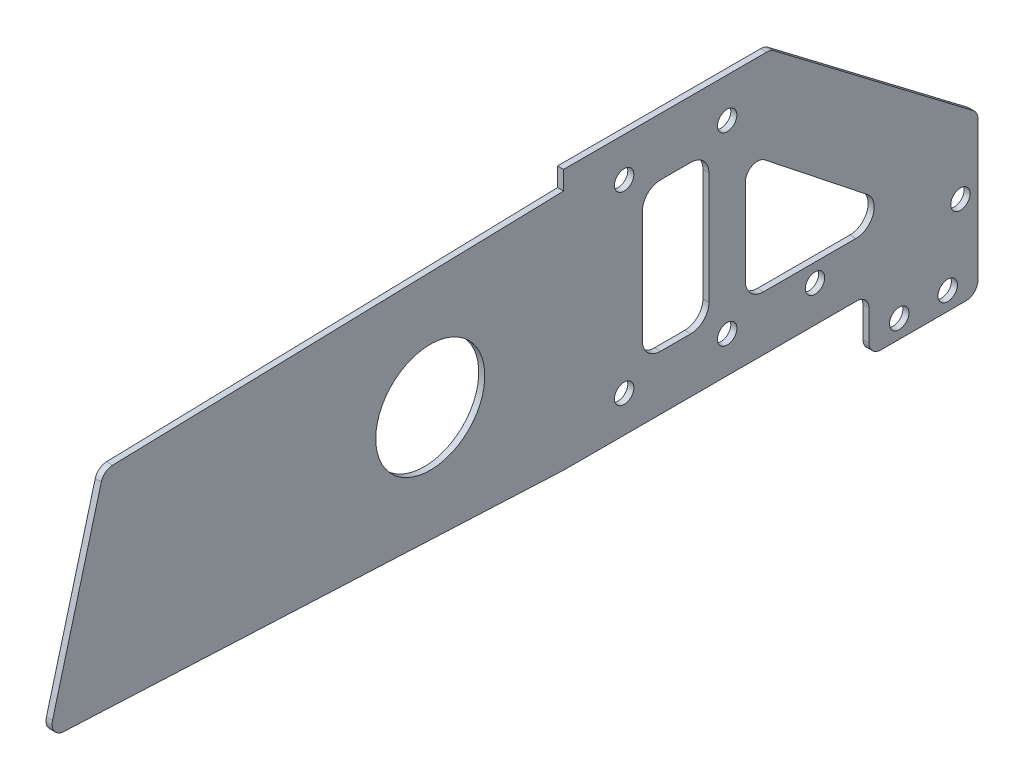
SolidWorks part; units mm, degrees
material "Hexcel AS4C (3000 丝)"
ref_plane "前视基准面" through (0, 0, 0) normal (0, 0, 1) x (1, 0, 0)
ref_plane "上视基准面" through (0, 0, 0) normal (0, 1, 0) x (1, 0, 0)
ref_plane "右视基准面" through (0, 0, 0) normal (1, 0, 0) x (0, 0, -1)
sketch "草图1" plane through (0, 0, 0) normal (1, 0, 0) x (0, 0, -1)
  line L0 (0, 0) -> (17, 0) construction
  line L1 (0, 0) -> (0, -30.5) construction
  line L2 (17, -30.5) -> (31.5, -30.5) construction
  line L4 (-10, 7.5) -> (48, 7.5)
  line L5 (-10, 7.5) -> (-10, -36.5)
  line L6 (-10, -36.5) -> (48, -36.5)
  line L7 (48, 7.5) -> (48, -36.5)
  line L8 (19, -36.5) -> (19, 7.5) construction
  line L9 (-10, -14.5) -> (48, -14.5) construction
  circle A0 centre (0, 0) radius 1.6
  circle A1 centre (17, 0) radius 1.6
  circle A2 centre (0, -30.5) radius 1.6
  circle A3 centre (17, -30.5) radius 1.6
  circle A4 centre (31.5, -30.5) radius 1.6
  point P257 (19, -14.5)
  dimension "D1" = 3.2
  dimension "D2" = 17
  dimension "D5" = 30.5
  dimension "D6" = 14.5
  dimension "D7" = 6
  dimension "D8" = 10
  dimension "D9" = 58
  dimension "D10" = 44
  dimension "D3" = 2
  dimension "D4" = 2
extrude "凸台-拉伸1" add sketch "草图1" along normal blind 1
sketch "草图2" plane through (1, 0, 0) normal (1, 0, 0) x (0, 0, -1)
  line L0 (-10, 7.5) -> (-10, -36.5) construction
  line L1 (48, 7.5) -> (-84.5, 7.5)
  line L2 (48, 7.5) -> (48, 97.5)
  line L3 (48, 97.5) -> (-84.5, 97.5)
  line L4 (-84.5, 7.5) -> (-84.5, 97.5)
  line L5 (-18.25, 97.5) -> (-18.25, 7.5) construction
  line L6 (48, 52.5) -> (-84.5, 52.5) construction
  point P288 (-18.25, 52.5)
  dimension "D1" = 90
  dimension "D2" = 74.5
extrude "凸台-拉伸2" add sketch "草图2" against normal up to surface (1 mm away) up to face at (0, -14.5, -19)
sketch "草图3" [suppressed] plane through (0, 0, 0) normal (-1, 0, 0) x (0, 0, 1)
  line L0 (86.5, 7.5) -> (62.3846, 97.5)
  line L1 (86.5, 97.5) -> (-48, 97.5) construction
  line L2 (62.3846, 97.5) -> (86.5, 97.5)
  line L3 (86.5, 97.5) -> (86.5, 7.5)
  dimension "D1" = 15
extrude "切除-拉伸1" [suppressed] cut sketch "草图3" against normal through all
sketch "草图4" [suppressed] plane through (0, 0, 0) normal (-1, 0, 0) x (0, 0, 1)
  line L0 (85.6962, 10.5) -> (-48, 10.5) construction
  line L1 (62.3846, 97.5) -> (86.5, 7.5) construction
  line L2 (-48, -36.5) -> (-48, 97.5) construction
  line L3 (12, 7.5) -> (86.5, 7.5) construction
  line L4 (71.5, 10.5) -> (51.5, 10.5) construction
  line L5 (63.1884, 94.5) -> (-48, 94.5) construction
  line L6 (62.3846, 97.5) -> (86.5, 7.5) construction
  line L7 (-48, -36.5) -> (-48, 97.5) construction
  line L8 (-48, 97.5) -> (62.3846, 97.5) construction
  circle A0 centre (71.5, 10.5) radius 1.6
  circle A1 centre (51.5, 10.5) radius 1.6
  circle A2 centre (12, 94.5) radius 1.6
  circle A3 centre (32, 94.5) radius 1.6
  dimension "D2" = 3.2
  dimension "D6" = 3.2
  dimension "D1" = 3
  dimension "D3" = 15
  dimension "D4" = 20
  dimension "D5" = 3
  dimension "D7" = 20
  dimension "D8" = 60
extrude "切除-拉伸2" [suppressed] cut sketch "草图4" against normal through all
sketch "草图5" [suppressed] plane through (1, 0, 0) normal (1, 0, 0) x (0, 0, -1)
  line L0 (-86.5, 7.5) -> (-12, 7.5) construction
  line L1 (-26.5, 60.5) -> (9.5, 60.5) construction
  line L2 (-26.5, 60.5) -> (-26.5, 24.5) construction
  line L3 (-26.5, 24.5) -> (9.5, 24.5) construction
  line L4 (9.5, 60.5) -> (9.5, 24.5) construction
  line L5 (-8.5, 24.5) -> (-8.5, 60.5) construction
  line L6 (-26.5, 42.5) -> (9.5, 42.5) construction
  circle A0 centre (-26.5, 60.5) radius 1.35
  circle A1 centre (9.5, 60.5) radius 1.35
  circle A2 centre (9.5, 24.5) radius 1.35
  circle A3 centre (-26.5, 24.5) radius 1.35
  point P0 (-8.5, 42.5)
  dimension "D2" = 2.7
  dimension "D1" = 36
  dimension "D3" = 35
  dimension "D4" = 60
extrude "切除-拉伸3" [suppressed] cut sketch "草图5" against normal through all
sketch "草图6" plane through (1, 0, 0) normal (1, 0, 0) x (0, 0, -1)
  line L0 (-84.5, 7.5) -> (-10, 7.5) construction
  line L1 (48, 97.5) -> (33, 97.5)
  line L2 (48, 97.5) -> (48, 7.5)
  line L3 (48, 7.5) -> (33, 7.5)
  line L4 (33, 97.5) -> (33, 7.5)
  line L5 (40.5, 7.5) -> (40.5, 97.5) construction
  line L6 (48, 52.5) -> (33, 52.5) construction
  point P304 (40.5, 52.5)
  dimension "D1" = 15
extrude "切除-拉伸4" cut sketch "草图6" against normal through all and the other way through all
sketch "草图7" plane through (1, 0, 0) normal (1, 0, 0) x (0, 0, -1)
  line L1 (0, 0) -> (17, 0) construction
  line L2 (0, 0) -> (0, -30.5) construction
  line L3 (0, -30.5) -> (17, -30.5) construction
  line L4 (17, 0) -> (17, -30.5) construction
  line L5 (8.5, -30.5) -> (8.5, 0) construction
  line L6 (0, -15.25) -> (17, -15.25) construction
  line L8 (4, -4) -> (13, -4)
  line L9 (4, -4) -> (4, -26.5)
  line L10 (4, -26.5) -> (13, -26.5)
  line L11 (13, -4) -> (13, -26.5)
  line L12 (8.5, -26.5) -> (8.5, -4) construction
  line L13 (4, -15.25) -> (13, -15.25) construction
  point P5 (8.5, -15.25)
  point P144 (8.5, -15.25)
  dimension "D1" = 4
  dimension "D2" = 4
extrude "切除-拉伸5" [suppressed] cut sketch "草图7" against normal through all
fillet "圆角1" [suppressed] radius 2
sketch "草图8" plane through (1, 0, 0) normal (1, 0, 0) x (0, 0, -1)
  line L0 (-10, 7.5) -> (33, 7.5)
  line L2 (48, 7.5) -> (-10, 7.5)
  line L3 (48, 7.5) -> (48, 6.5)
  line L4 (48, 6.5) -> (-10, 6.5)
  line L5 (-10, 7.5) -> (-10, 6.5)
  line L7 (-10, 7.5) -> (-10, -36.5) construction
  line L14 (-84.5, 97.5) -> (-84.5, 7.5)
  line L15 (33, 7.5) -> (33, 97.5)
  line L16 (-84.5, 97.5) -> (-84.5, 7.5)
  line L17 (33, 97.5) -> (-84.5, 97.5)
  line L21 (-84.5, 7.5) -> (-10, 7.5)
  line L22 (-10, 7.5) -> (-10, -36.5)
  line L24 (-10, -36.5) -> (48, -36.5)
  line L26 (48, -36.5) -> (48, 7.5)
  line L28 (48, 7.5) -> (33, 7.5)
  line L29 (33, 7.5) -> (33, 97.5)
  line L31 (33, 97.5) -> (-84.5, 97.5)
  line L35 (-84.5, 7.5) -> (-10, 7.5)
  dimension "D2" = 1
  dimension "D1" = 0
extrude "切除-拉伸6" cut sketch "草图8" against normal through all
sketch "草图9" plane through (1, 0, 0) normal (1, 0, 0) x (0, 0, -1)
  line L0 (-10, 3.4) -> (-85.9165, 1.4)
  line L1 (-10, 6.5) -> (-10, -36.5) construction
  line L2 (-85.9165, 1.4) -> (-95, -32.5)
  line L3 (-95, -32.5) -> (-10, -32.5) construction
  line L4 (-10, 3.4) -> (-10, -32.5)
  line L5 (48, 6.5) -> (-10, 6.5) construction
  line L7 (-10, -36.5) -> (48, -36.5) construction
  line L8 (-95, -32.5) -> (-10, -36.5)
  line M20 (-10, 6.5) -> (-10, -36.5)
  dimension "D1" = 3.1
  dimension "D2" = 85
  dimension "D3" = 75
  dimension "D4" = 4
  dimension "D5" = 2
extrude "凸台-拉伸3" add sketch "草图9" against normal up to surface (1 mm away) contours L2 L3 L0 M20 | L3 L8 M20 up to face at (0, -30.5, -33.1)
sketch "草图10" plane through (1, 0, 0) normal (1, 0, 0) x (0, 0, -1)
  line L3 (48, 6.5) -> (-10, 6.5) construction
  line L4 (40.4, -45.5) -> (58.4, -45.5)
  line L5 (40.4, -36.5) -> (40.4, -45.5)
  line L6 (-10, -36.5) -> (48, -36.5) construction
  line L8 (58.4, -45.5) -> (58.4, 6.5)
  line L9 (58.4, 6.5) -> (48, 6.5)
  line L11 (48, -36.5) -> (48, 6.5) construction
  line L12 (48, -36.5) -> (48, 6.5)
  line L13 (40.4, -36.5) -> (48, -36.5)
  dimension "D1" = 10.4
  dimension "D2" = 9
  dimension "D3" = 18
extrude "凸台-拉伸4" add sketch "草图10" against normal up to surface (1 mm away) up to face at (0, -30.5, -33.1)
sketch "草图11" plane through (1, 0, 0) normal (1, 0, 0) x (0, 0, -1)
  line L1 (40.4, -45.5) -> (58.4, -45.5) construction
  line L2 (58.4, -45.5) -> (58.4, 6.5) construction
  circle A0 centre (45.4, -42.5) radius 1.6
  circle A1 centre (53.4, -42.5) radius 1.6
  dimension "D1" = 3.2
  dimension "D2" = 5
  dimension "D3" = 8
  dimension "D4" = 3
extrude "切除-拉伸7" cut sketch "草图11" against normal through all
fillet "圆角4" [suppressed] radius 1
sketch "草图13" plane through (1, 0, 0) normal (1, 0, 0) x (0, 0, -1)
  line L0 (24.2, 6.5) -> (58.4, -19.5)
  line L1 (58.4, 6.5) -> (-10, 6.5) construction
  line L2 (58.4, -45.5) -> (58.4, 6.5) construction
  line L3 (58.4, -19.5) -> (58.4, 6.5)
  line L4 (58.4, 6.5) -> (24.2, 6.5)
extrude "切除-拉伸8" cut sketch "草图13" against normal through all
fillet "圆角3" radius 2 7 edges at (0.5, 1.4, 85.9165) (0.5, -36.5, -40.4) (0.5, -45.5, -58.4) (0.5, -45.5, -40.4) (0.5, -32.5, 95) (0.5, -19.5, -58.4) (0.5, 6.5, -24.2)
sketch "草图14" plane through (1, 0, 0) normal (1, 0, 0) x (0, 0, -1)
  line L0 (31.5, -30.5) -> (-49968.5, -30.5) construction
  line L1 (58.4, -43.5) -> (58.4, -20.4919) construction
  circle A0 centre (55.5, -30.5) radius 1.6
  circle A1 centre (31.5, -30.5) radius 1.6 construction
  dimension "D1" = 2.9
extrude "切除-拉伸9" cut sketch "草图14" against normal through all
sketch "草图15" plane through (0, 0, 0) normal (-1, 0, 0) x (0, 0, 1)
  line L0 (10, -36.5) -> (-38.4, -36.5) construction
  line L2 (10, 6.5) -> (10, 3.4) construction
  circle A0 centre (32, -16.5) radius 9
  dimension "D1" = 18
  dimension "D2" = 20
  dimension "D3" = 22
extrude "切除-拉伸10" cut sketch "草图15" against normal through all contours A0
sketch "草图16" plane through (0, 0, 0) normal (-1, 0, 0) x (0, 0, 1)
  line L0 (-17, 0) -> (-17, -30.5) construction
  line L1 (-17, -30.5) -> (0, -30.5) construction
  line L2 (0, -30.5) -> (0, 0) construction
  line L3 (0, 0) -> (-17, 0) construction
  line L4 (-17, -30.5) -> (-31.5, -30.5) construction
  line L5 (-31.5, -30.5) -> (-55.5, -30.5) construction
  line L6 (-55.5, -30.5) -> (-17, 0) construction
  line L7 (-40.1267, -22.1485) -> (-23.2419, -8.7722)
  line L12 (-14, -6) -> (-14, -24.5)
  line L13 (-11, -27.5) -> (-6, -27.5)
  line L14 (-3, -24.5) -> (-3, -6)
  line L15 (-6, -3) -> (-11, -3)
  line L22 (-14, -27.5) -> (-3, -27.5) construction
  line L23 (-3, -27.5) -> (-3, -3) construction
  line L24 (-14, -3) -> (-14, -27.5) construction
  line L25 (-3, -3) -> (-14, -3) construction
  line L26 (-20, -10.3399) -> (-20, -24.5)
  line L27 (-23, -27.5) -> (-31.5, -27.5)
  line L28 (-31.5, -27.5) -> (-38.2638, -27.5)
  line L29 (-20, -6.2039) -> (-20, -27.5) construction
  line L30 (-20, -27.5) -> (-31.5, -27.5) construction
  line L31 (-46.8819, -27.5) -> (-20, -6.2039) construction
  line L32 (-31.5, -27.5) -> (-46.8819, -27.5) construction
  arc A0 (-6, -27.5) -> (-3, -24.5) centre (-6, -24.5) ccw
  arc A1 (-14, -24.5) -> (-11, -27.5) centre (-11, -24.5) ccw
  arc A2 (-3, -6) -> (-6, -3) centre (-6, -6) ccw
  arc A3 (-14, -6) -> (-11, -3) centre (-11, -6) cw
  arc A12 (-20, -24.5) -> (-23, -27.5) centre (-23, -24.5) cw
  arc A13 (-40.1267, -22.1485) -> (-38.2638, -27.5) centre (-38.2638, -24.5) ccw
  arc A14 (-23.2419, -8.7722) -> (-20, -10.3399) centre (-22, -10.3399) cw
  dimension "D4" = 3
  dimension "D5" = 2
  dimension "D3" = 3
  dimension "D1" = 3
  dimension "D2" = 3
extrude "切除-拉伸11" cut sketch "草图16" against normal through all
